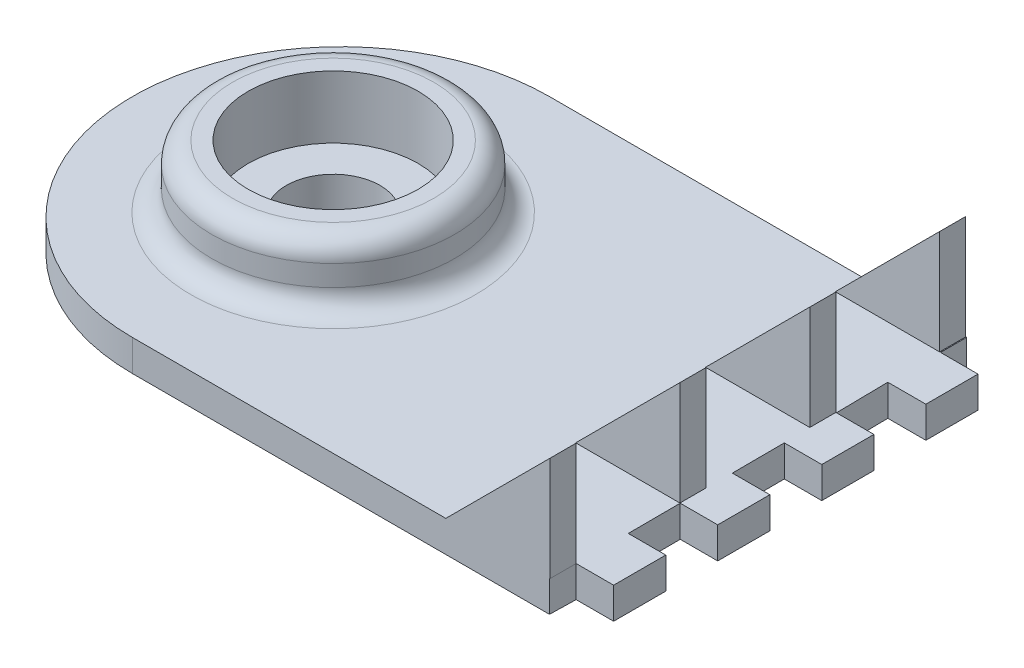
SolidWorks part; units mm, degrees
ref_plane "Front Plane" through (0, 0, 0) normal (0, 0, 1) x (1, 0, 0)
ref_plane "Top Plane" through (0, 0, 0) normal (0, 1, 0) x (1, 0, 0)
ref_plane "Right Plane" through (0, 0, 0) normal (1, 0, 0) x (0, 0, -1)
sketch "Sketch1" plane through (0, 0, 0) normal (0, 1, 0) x (1, 0, 0)
  line L0 (20, 17.5) -> (23.5928, 17.5)
  line L1 (-20, 20) -> (20, 20)
  line L3 (-20, -20) -> (20, -20)
  line L4 (20, 20) -> (20, 17.5)
  line L5 (-20, 20) -> (20, -20) construction
  line L6 (-20, -20) -> (20, 20) construction
  line L7 (20.0194, 7.5) -> (23.6123, 7.5)
  line L8 (23.5928, 12.5) -> (19.9445, 12.5)
  line L9 (23.5928, 17.5) -> (23.5928, 12.5)
  line L10 (23.6123, 7.5) -> (23.6123, 2.5)
  line L11 (23.6123, 2.5) -> (20.0194, 2.5)
  line L12 (20.0388, -2.5) -> (23.6317, -2.5)
  line L13 (23.6317, -2.5) -> (23.6317, -7.5)
  line L14 (23.6317, -7.5) -> (20.0388, -7.5)
  line L15 (20.0583, -12.4999) -> (23.6511, -12.4999)
  line L16 (23.6511, -12.4999) -> (23.6511, -17.4999)
  line L17 (23.6511, -17.4999) -> (20.0583, -17.4999)
  line L19 (19.9445, 12.5) -> (20.0194, 7.5)
  line L20 (20.0194, 2.5) -> (20.0388, -2.5)
  line L21 (20, -20) -> (20.0583, -17.4999)
  line L22 (20.0583, -12.4999) -> (20.0388, -7.5)
  arc A0 (-20, -20) -> (-20, 20) centre (-20, 0) cw
  point P0 (0, 0)
  dimension "D3" = 20
  dimension "D1" = 40
  dimension "D2" = 40
  dimension "D4" = 2.5
  dimension "D5" = 5
  dimension "D6" = 4
extrude "Boss-Extrude1" add sketch "Sketch1" along normal blind 3
ref_plane "rib plane" through (0, 0, 20) normal (0, 0, 1) x (1, 0, 0)
sketch "Sketch2" plane through (0, 0, 20) normal (0, 0, 1) x (1, 0, 0)
  line L0 (20.0583, 3) -> (20.0583, 13)
  line L1 (20.0583, 3) -> (10.0583, 3)
  line L2 (-20, 3) -> (20, 3) construction
  line L3 (20.0583, 13) -> (10.0583, 3)
  dimension "D1" = 10
  dimension "D2" = 10
extrude "Boss-Extrude3" add sketch "Sketch2" against normal blind 2.5
pattern_linear "LPattern2" count 4 spacing 12.5 along (-0.0039, 0, -1) of "Boss-Extrude3"
sketch "Sketch3" plane through (0, 3, 0) normal (0, 1, 0) x (1, 0, 0)
  circle A0 centre (-20.7417, 0) radius 11.65
  circle A1 centre (-20.7417, 0) radius 8.15
  dimension "D1" = 16.3
  dimension "D2" = 3.5
extrude "Boss-Extrude4" add sketch "Sketch3" along normal blind 6
sketch "Sketch4" plane through (0, 0, 0) normal (0, 1, 0) x (1, 0, 0)
  circle A0 centre (-20.7417, 0) radius 4.5
extrude "Cut-Extrude2" cut sketch "Sketch4" along normal through all
fillet "Fillet1" radius 2 1 edges at (-20.7417, 3, -11.65)
fillet "Fillet2" radius 2 1 edges at (-20.7417, 9, 11.65)
